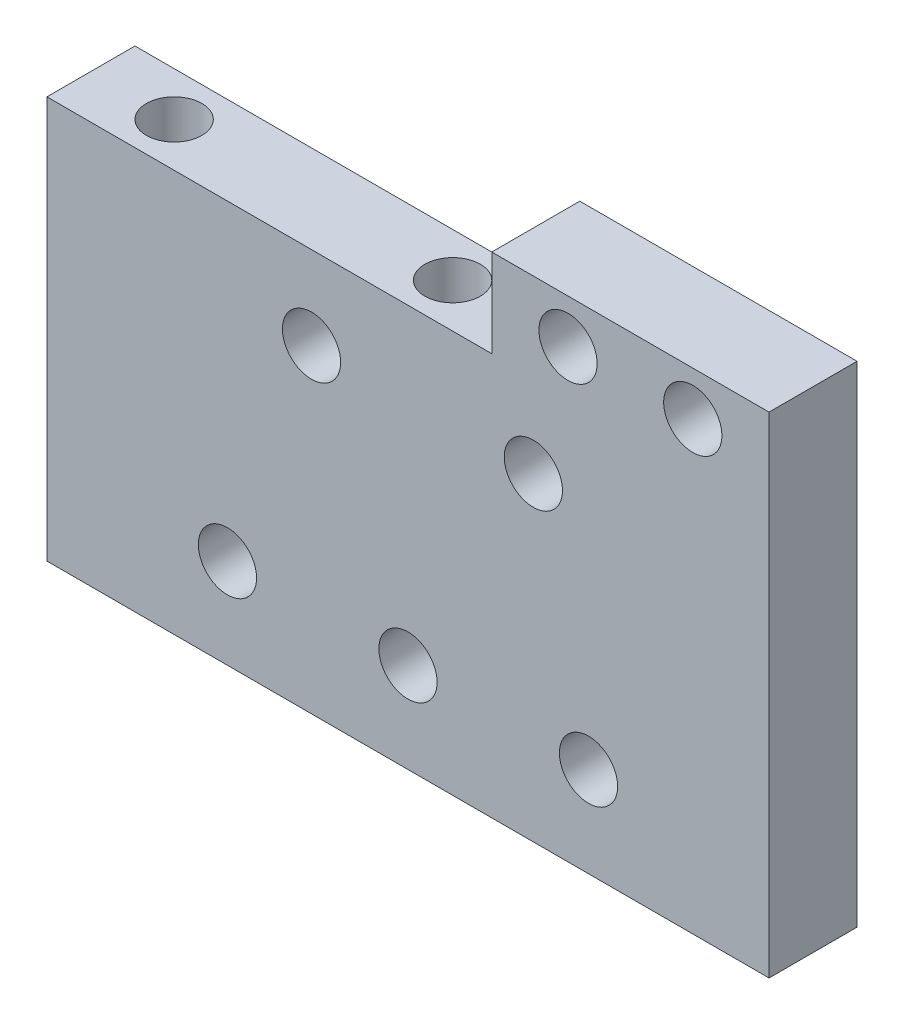
SolidWorks part; units mm, degrees
material "Plain Carbon Steel"
ref_plane "Front Plane" through (0, 0, 0) normal (0, 0, 1) x (1, 0, 0)
ref_plane "Top Plane" through (0, 0, 0) normal (0, 1, 0) x (1, 0, 0)
ref_plane "Right Plane" through (0, 0, 0) normal (1, 0, 0) x (0, 0, -1)
sketch "Sketch1" plane through (0, 0, 0) normal (0, 0, 1) x (1, 0, 0)
  line L0 (110, 6.35) -> (110, 0) construction
  line L1 (90, 6.35) -> (110, 6.35)
  line L2 (90, 6.35) -> (90, 0)
  line L3 (57.9145, -29) -> (110, -29)
  line L4 (110, 6.35) -> (110, -29)
  line L5 (90, 0) -> (57.9145, 0)
  line L7 (57.9145, 0) -> (57.9145, -29)
  circle A0 centre (95.5, 3.175) radius 2.1
  circle A1 centre (104.5, 3.175) radius 2.1
  circle A2 centre (95.5, 3.175) radius 2.1 construction
  circle A3 centre (104.5, 3.175) radius 2.1 construction
  dimension "D2" = 4.2
  dimension "D1" = 29
extrude "Boss-Extrude1" add sketch "Sketch1" along normal blind 6.35
sketch "Sketch2" plane through (0, 0, 6.35) normal (0, 0, 1) x (1, 0, 0)
  circle A0 centre (70.9359, -22.5) radius 2.1 construction
  circle A1 centre (83.9573, -22.5) radius 2.1 construction
  circle A2 centre (96.9786, -22.5) radius 2.1 construction
  circle A3 centre (93, -6) radius 2.1 construction
  circle A4 centre (77, -6) radius 2.1 construction
  circle A5 centre (70.9359, -22.5) radius 2.1
  circle A6 centre (83.9573, -22.5) radius 2.1
  circle A7 centre (96.9786, -22.5) radius 2.1
  circle A8 centre (93, -6) radius 2.1
  circle A9 centre (77, -6) radius 2.1
extrude "Cut-Extrude1" cut sketch "Sketch2" against normal through all
sketch "Sketch3" plane through (0, 0, 0) normal (0, 1, 0) x (-1, 0, 0)
  circle A0 centre (-84, 3.175) radius 2
  circle A1 centre (-63.9145, 3.175) radius 2
  circle A2 centre (-63.9145, 3.175) radius 2.1 construction
  dimension "D1" = 4
extrude "Cut-Extrude2" cut sketch "Sketch3" against normal blind 8
